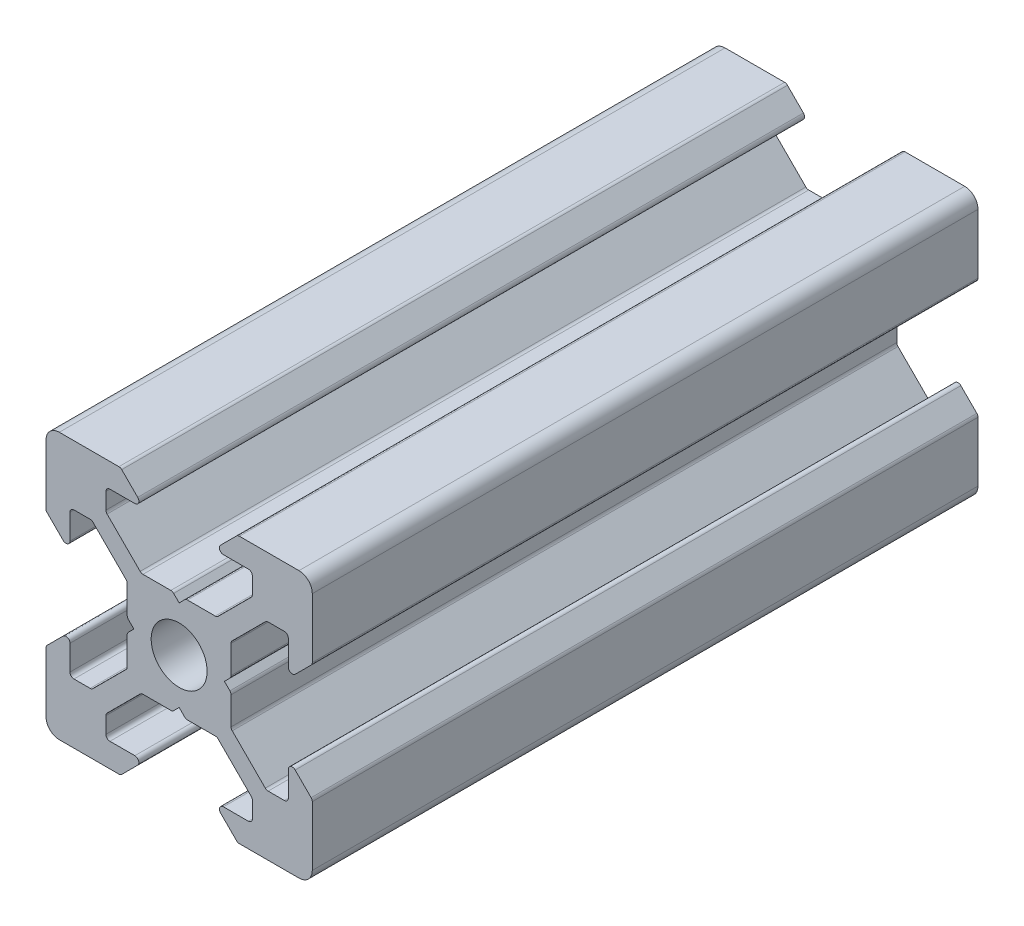
SolidWorks part; units mm, degrees
material "1060 СплавА"
ref_plane "Спереди" through (0, 0, 0) normal (0, 0, 1) x (1, 0, 0)
ref_plane "Сверху" through (0, 0, 0) normal (0, 1, 0) x (1, 0, 0)
ref_plane "Справа" through (0, 0, 0) normal (1, 0, 0) x (0, 0, -1)
sketch "Эскиз1" plane through (0, 0, 0) normal (0, 0, 1) x (1, 0, 0)
  line L0 (0, -12.9654) -> (0, 12.9654) construction
  line L1 (-12.9654, 0) -> (12.9654, 0) construction
  line L2 (0, 0) -> (-18.3359, 18.3359) construction
  line L3 (-10, 10) -> (-4.4, 10)
  line L4 (-4.4, 10) -> (-2.6, 8.2)
  line L5 (-2.6, 8.2) -> (-5.4993, 8.2)
  line L6 (-5.4993, 8.2) -> (-5.4993, 6.56)
  line L7 (-5.4993, 6.56) -> (-2.84, 3.9007)
  line L8 (-2.84, 3.9007) -> (-0.5, 3.9007)
  line L9 (-0.5, 3.9007) -> (0, 3.4007)
  line L10 (-3.9007, 0.5) -> (-3.4007, 0)
  line L11 (-3.9007, 2.84) -> (-3.9007, 0.5)
  line L12 (-6.56, 5.4993) -> (-3.9007, 2.84)
  line L13 (-8.2, 5.4993) -> (-6.56, 5.4993)
  line L14 (-8.2, 2.6) -> (-8.2, 5.4993)
  line L15 (-10, 4.4) -> (-8.2, 2.6)
  line L16 (-10, 10) -> (-10, 4.4)
  line L17 (10, 10) -> (10, 4.4)
  line L18 (10, 4.4) -> (8.2, 2.6)
  line L19 (8.2, 2.6) -> (8.2, 5.4993)
  line L20 (8.2, 5.4993) -> (6.56, 5.4993)
  line L21 (6.56, 5.4993) -> (3.9007, 2.84)
  line L22 (3.9007, 2.84) -> (3.9007, 0.5)
  line L23 (3.9007, 0.5) -> (3.4007, 0)
  line L24 (0.5, 3.9007) -> (0, 3.4007)
  line L25 (2.84, 3.9007) -> (0.5, 3.9007)
  line L26 (5.4993, 6.56) -> (2.84, 3.9007)
  line L27 (5.4993, 8.2) -> (5.4993, 6.56)
  line L28 (2.6, 8.2) -> (5.4993, 8.2)
  line L29 (4.4, 10) -> (2.6, 8.2)
  line L30 (10, 10) -> (4.4, 10)
  line L31 (3.9007, -0.5) -> (3.4007, 0)
  line L32 (-3.9007, -0.5) -> (-3.4007, 0)
  line L33 (10, -10) -> (4.4, -10)
  line L34 (4.4, -10) -> (2.6, -8.2)
  line L35 (2.6, -8.2) -> (5.4993, -8.2)
  line L36 (5.4993, -8.2) -> (5.4993, -6.56)
  line L37 (5.4993, -6.56) -> (2.84, -3.9007)
  line L38 (2.84, -3.9007) -> (0.5, -3.9007)
  line L39 (0.5, -3.9007) -> (0, -3.4007)
  line L40 (3.9007, -2.84) -> (3.9007, -0.5)
  line L41 (6.56, -5.4993) -> (3.9007, -2.84)
  line L42 (8.2, -5.4993) -> (6.56, -5.4993)
  line L43 (8.2, -2.6) -> (8.2, -5.4993)
  line L44 (10, -4.4) -> (8.2, -2.6)
  line L45 (10, -10) -> (10, -4.4)
  line L46 (-10, -10) -> (-10, -4.4)
  line L47 (-10, -4.4) -> (-8.2, -2.6)
  line L48 (-8.2, -2.6) -> (-8.2, -5.4993)
  line L49 (-8.2, -5.4993) -> (-6.56, -5.4993)
  line L50 (-6.56, -5.4993) -> (-3.9007, -2.84)
  line L51 (-3.9007, -2.84) -> (-3.9007, -0.5)
  line L52 (-0.5, -3.9007) -> (0, -3.4007)
  line L53 (-2.84, -3.9007) -> (-0.5, -3.9007)
  line L54 (-5.4993, -6.56) -> (-2.84, -3.9007)
  line L55 (-5.4993, -8.2) -> (-5.4993, -6.56)
  line L56 (-2.6, -8.2) -> (-5.4993, -8.2)
  line L57 (-4.4, -10) -> (-2.6, -8.2)
  line L58 (-10, -10) -> (-4.4, -10)
  circle A0 centre (0, 0) radius 2.1
  dimension "D5" = 2.6
  dimension "D10" = 4.2
  dimension "D2" = 10
  dimension "D3" = 1.64
  dimension "D4" = 1.5
  dimension "D6" = 1.8
  dimension "D7" = 2.84
  dimension "D8" = 0.5
  dimension "D9" = 45
extrude "Бобышка-Вытянуть1" add sketch "Эскиз1" along normal blind 50
fillet "Скругление1" radius 1 4 edges at (-10, -10, 25) (10, -10, 25) (10, 10, 25) (-10, 10, 25)
fillet "Скругление2" radius 0.3 47 edges at (10, 4.4, 25) (8.2, 2.6, 25) (8.2, 5.4993, 25) (6.56, 5.4993, 25) (3.9007, 2.84, 25) (3.9007, 0.5, 25) (3.9007, -0.5, 25) (3.9007, -2.84, 25) (6.56, -5.4993, 25) (10, -4.4, 25) (8.2, -5.4993, 25) (8.2, -2.6, 25) (4.4, -10, 25) (2.6, -8.2, 25) (5.4993, -8.2, 25) (5.4993, -6.56, 25) (2.84, -3.9007, 25) (0.5, -3.9007, 25) (-0.5, -3.9007, 25) (-2.84, -3.9007, 25) (-5.4993, -6.56, 25) (-5.4993, -8.2, 25) (-2.6, -8.2, 25) (-4.4, -10, 25) (-10, -4.4, 25) (-8.2, -2.6, 25) (-8.2, -5.4993, 25) (-6.56, -5.4993, 25) (-3.9007, -2.84, 25) (-3.9007, -0.5, 25) (-3.9007, 0.5, 25) (-3.9007, 2.84, 25) (-6.56, 5.4993, 25) (-8.2, 5.4993, 25) (-8.2, 2.6, 25) (-4.4, 10, 25) (-2.6, 8.2, 25) (-5.4993, 8.2, 25) (-5.4993, 6.56, 25) (-2.84, 3.9007, 25) (-0.5, 3.9007, 25) (0.5, 3.9007, 25) (2.84, 3.9007, 25) (5.4993, 6.56, 25) (5.4993, 8.2, 25) (2.6, 8.2, 25) (4.4, 10, 25)
